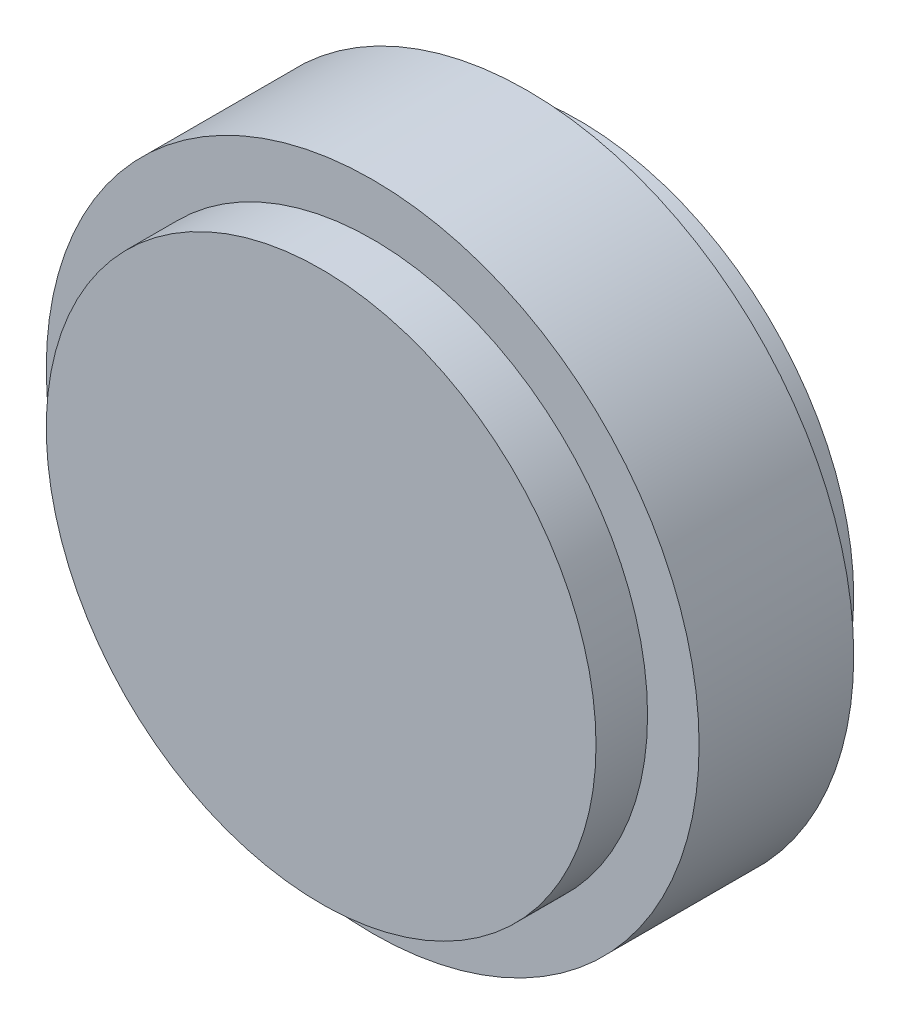
SolidWorks part; units mm, degrees
material "Molybdenum"
ref_plane "Front" through (0, 0, 0) normal (0, 0, 1) x (1, 0, 0)
ref_plane "Top" through (0, 0, 0) normal (0, 1, 0) x (1, 0, 0)
ref_plane "Right" through (0, 0, 0) normal (1, 0, 0) x (0, 0, -1)
sketch "Sketch2" plane through (0, 0, 0) normal (1, 0, 0) x (0, 0, -1)
  line L0 (0, 0) -> (67.6083, 0) construction
  line L1 (7.5, 0) -> (7.5, 19) construction
  line L2 (0, 0) -> (15, 0)
  line L3 (0, 0) -> (0, 16)
  line L4 (0, 16) -> (3, 16)
  line L5 (15, 0) -> (15, 16)
  line L7 (3, 16) -> (3, 19)
  line L8 (3, 19) -> (12, 19)
  line L9 (12, 16) -> (12, 19)
  line L10 (12, 16) -> (15, 16)
  dimension "D1" = 16
  dimension "D2" = 3
  dimension "D3" = 15
revolve "Revolve1" add sketch "Sketch2" angle 360 about L0
